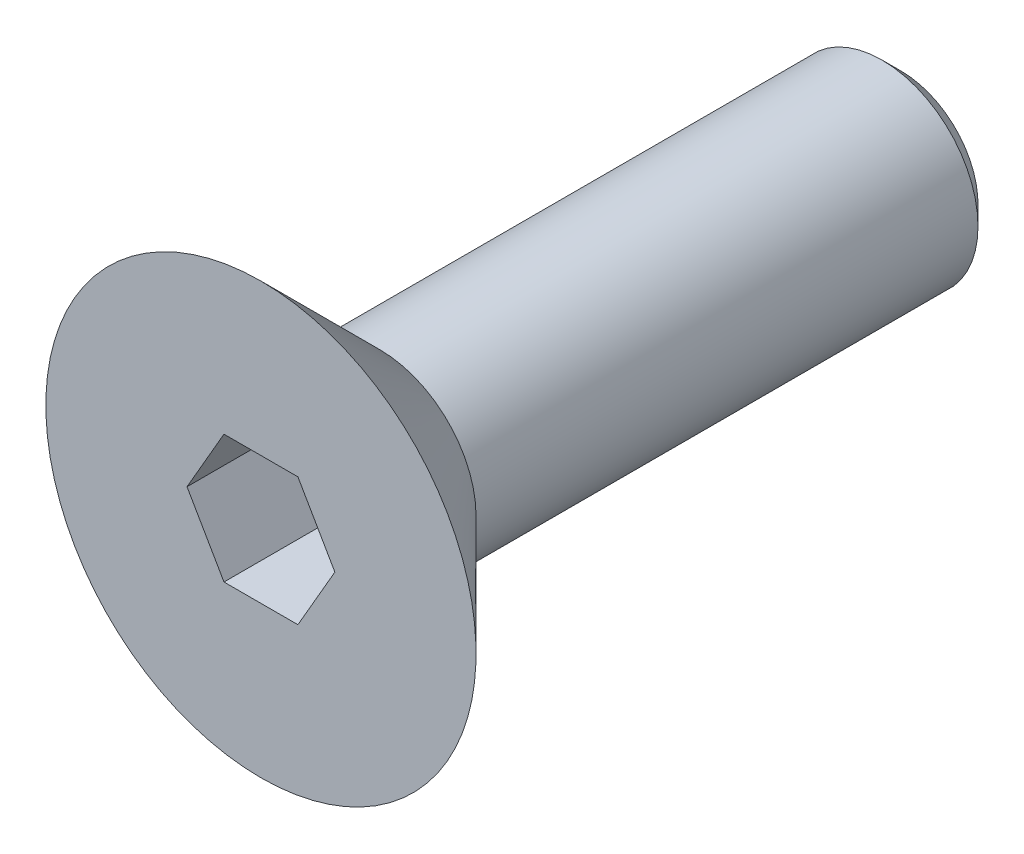
SolidWorks part; units mm, degrees
material "Простая углеродистая сталь"
ref_plane "Спереди" through (0, 0, 0) normal (0, 0, 1) x (1, 0, 0)
ref_plane "Сверху" through (0, 0, 0) normal (0, 1, 0) x (1, 0, 0)
ref_plane "Справа" through (0, 0, 0) normal (1, 0, 0) x (0, 0, -1)
sketch "Эскиз1" plane through (0, 0, 0) normal (1, 0, 0) x (0, 0, -1)
  line L0 (0, 0) -> (0, 3.36)
  line L1 (0, 3.36) -> (1.86, 1.5)
  line L2 (1.86, 1.5) -> (10, 1.5)
  line L3 (10, 1.5) -> (10, 0)
  line L4 (10, 0) -> (0, 0)
  dimension "D1" = 1.5
  dimension "D2" = 10
  dimension "D3" = 1.86
  dimension "D4" = 3.36
revolve "Повернуть1" add sketch "Эскиз1" angle 360 about L4
sketch "Эскиз2" plane through (0, 0, 0) normal (0, 0, 1) x (1, 0, 0)
  line L0 (0, 0) -> (0.4854, 0) construction
  line L1 (1.1547, 0) -> (0.5774, 1)
  line L2 (0.5774, 1) -> (-0.5774, 1)
  line L3 (-0.5774, 1) -> (-1.1547, 0)
  line L4 (-1.1547, 0) -> (-0.5774, -1)
  line L5 (-0.5774, -1) -> (0.5774, -1)
  line L6 (0.5774, -1) -> (1.1547, 0)
  circle A0 centre (0, 0) radius 1 construction
  dimension "D1" = 2
  dimension "D2" = 60
extrude "Вырез-Вытянуть1" cut sketch "Эскиз2" against normal blind 2
chamfer "Фаска1" distance 0.3 angle 45 1 edges at (0, 1.5, -10)
